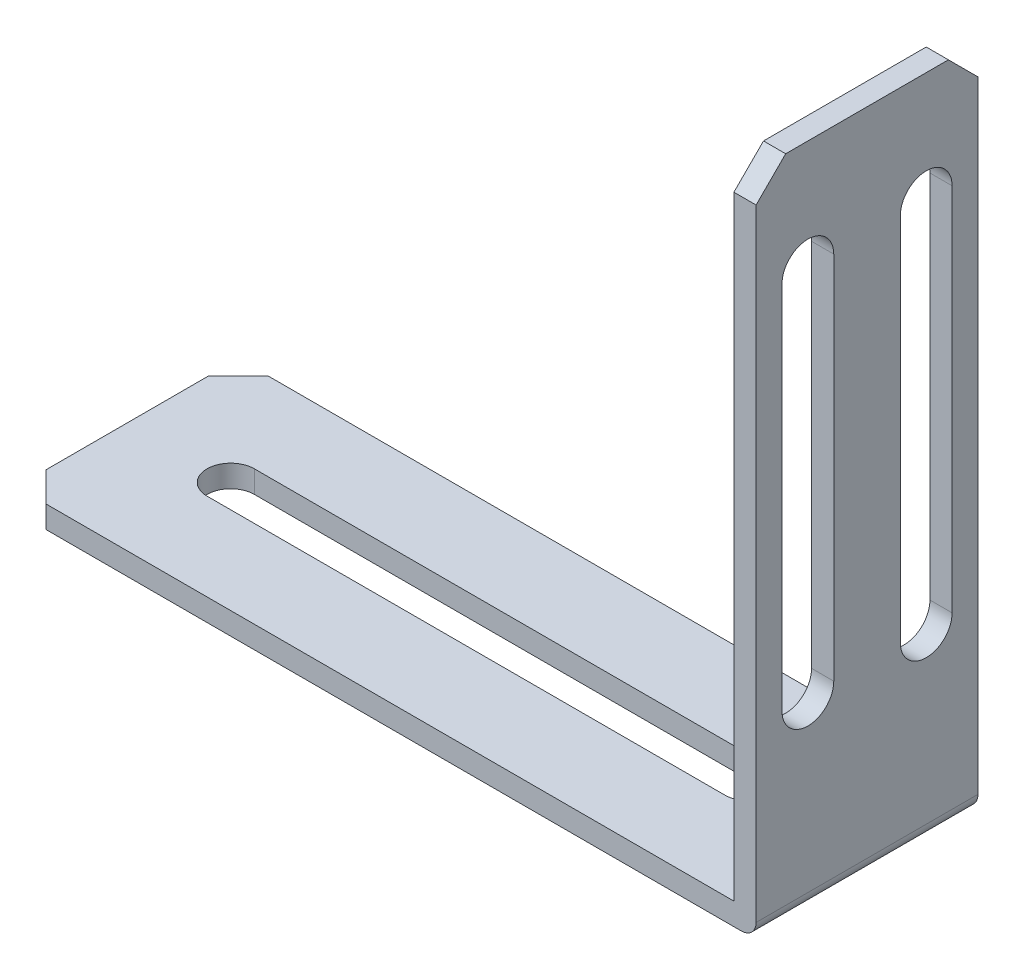
SolidWorks part; units mm, degrees
ref_plane "Front Plane" through (0, 0, 0) normal (0, 0, 1) x (1, 0, 0)
ref_plane "Top Plane" through (0, 0, 0) normal (0, 1, 0) x (1, 0, 0)
ref_plane "Right Plane" through (0, 0, 0) normal (1, 0, 0) x (0, 0, -1)
sketch "Sketch1" plane through (0, 0, 0) normal (0, 0, 1) x (1, 0, 0)
  line L0 (-218.8406, 0) -> (-170.3406, 0)
  line L1 (-170.3406, 0) -> (-170.3406, 43.5)
  line L2 (-170.3406, 43.5) -> (-168.8406, 43.5)
  line L3 (-168.8406, 43.5) -> (-168.8406, -1.5)
  line L4 (-168.8406, -1.5) -> (-218.8406, -1.5)
  line L5 (-218.8406, -1.5) -> (-218.8406, 0)
  dimension "D1" = 1.5
  dimension "D2" = 1.5
  dimension "D3" = 50
  dimension "D4" = 45
extrude "Boss-Extrude1" add sketch "Sketch1" along normal blind 15
sketch "Sketch2" plane through (0, 0, 0) normal (0, 1, 0) x (1, 0, 0)
  line L0 (-218.8406, -15) -> (-218.8406, 0) construction
  line L1 (-176.8548, -9.1) -> (-211.8548, -9.1)
  line L3 (-176.8548, -5.9) -> (-211.8548, -5.9)
  arc A0 (-211.8548, -5.9) -> (-211.8548, -9.1) centre (-211.8548, -7.5) ccw
  arc A1 (-176.8548, -9.1) -> (-176.8548, -5.9) centre (-176.8548, -7.5) ccw
  point P0 (-194.3548, -7.5)
  point P7 (-218.8406, -7.5)
  point P9 (0, 0)
  dimension "D1" = 3.2
  dimension "D2" = 35
extrude "Cut-Extrude1" cut sketch "Sketch2" against normal through all
sketch "Sketch3" plane through (-170.3406, 0, 0) normal (-1, 0, 0) x (0, 0, 1)
  line L2 (1.75, 36) -> (1.75, 11)
  line L4 (5.25, 36) -> (5.25, 11)
  line L12 (9.75, 36) -> (9.75, 11)
  line L14 (13.25, 36) -> (13.25, 11)
  arc A0 (5.25, 36) -> (1.75, 36) centre (3.5, 36) ccw
  arc A1 (1.75, 11) -> (5.25, 11) centre (3.5, 11) ccw
  arc A2 (9.75, 11) -> (13.25, 11) centre (11.5, 11) ccw
  arc A3 (13.25, 36) -> (9.75, 36) centre (11.5, 36) ccw
  point P0 (3.5, 23.5)
  point P18 (11.5, 23.5)
  dimension "D2" = 3.5
  dimension "D4" = 25
extrude "Cut-Extrude2" cut sketch "Sketch3" against normal through all
chamfer "Chamfer1" distance 2 angle 45 4 edges at (-169.5906, 43.5, 0) (-169.5906, 43.5, 15) (-218.8406, -0.75, 15) (-218.8406, -0.75, 0)
fillet "Fillet1" radius 1 1 edges at (-168.8406, -1.5, 7.5)
